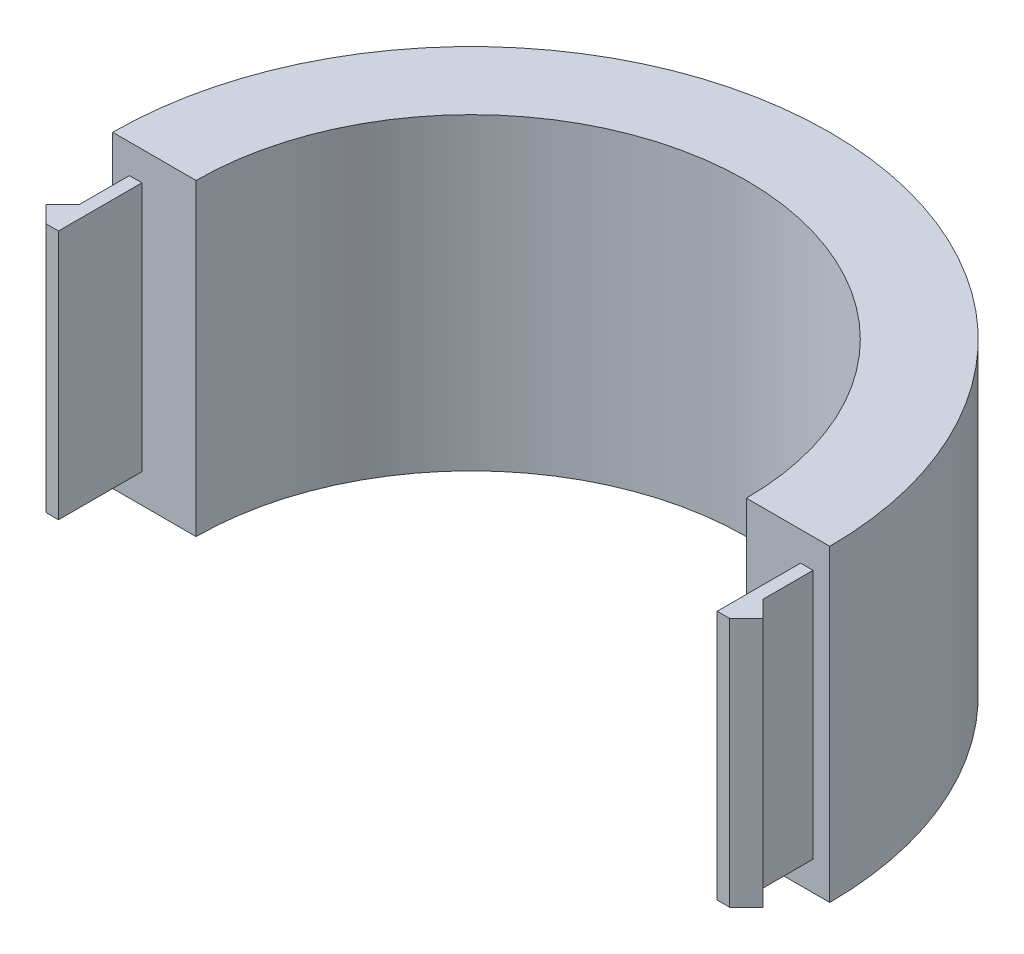
SolidWorks part; units mm, degrees
ref_plane "Front Plane" through (0, 0, 0) normal (0, 0, 1) x (1, 0, 0)
ref_plane "Top Plane" through (0, 0, 0) normal (0, 1, 0) x (1, 0, 0)
ref_plane "Right Plane" through (0, 0, 0) normal (1, 0, 0) x (0, 0, -1)
sketch "Sketch1" plane through (0, 0, 0) normal (0, 1, 0) x (1, 0, 0)
  line L0 (-43, 0) -> (43, 0)
  circle A0 centre (0, 0) radius 33
  circle A1 centre (0, 0) radius 43
  dimension "D1" = 66
  dimension "D2" = 10
extrude "Boss-Extrude1" add sketch "Sketch1" along normal blind 37 contours L0 A1 A0
ref_plane "Plane1" through (0, 18.5, 0) normal (0, 1, 0) x (1, 0, 0)
sketch "Sketch3" plane through (0, 18.5, 0) normal (0, 1, 0) x (1, 0, 0)
  line L0 (-39.5, 0) -> (-39.5, -10)
  line L1 (-39.5, 0) -> (-41, 0)
  line L2 (-39.5, -10) -> (-41, -10)
  line L3 (-41, 0) -> (-41, -10)
  line L4 (-39.5, 0) -> (-41, -10) construction
  line L5 (-39.5, -10) -> (-41, 0) construction
  line L6 (-43, 0) -> (-33, 0) construction
  line L7 (-41, -10) -> (-43, -8)
  line L8 (-43, -8) -> (-41, -6)
  line L9 (-43, -8) -> (-41, -8) construction
  point P1 (-40.25, -5)
  point P8 (-38, 0)
  dimension "D1" = 1.5
  dimension "D2" = 10
  dimension "D3" = 45
  dimension "D4" = 45
  dimension "D5" = 2
  dimension "D6" = 2
extrude "Boss-Extrude2" add sketch "Sketch3" along normal mid plane 30 contours L1 L3 L2 L0 | L8 L7 L3
mirror "Mirror1" about plane through (0, 0, 0) normal (1, 0, 0) of "Boss-Extrude2"
